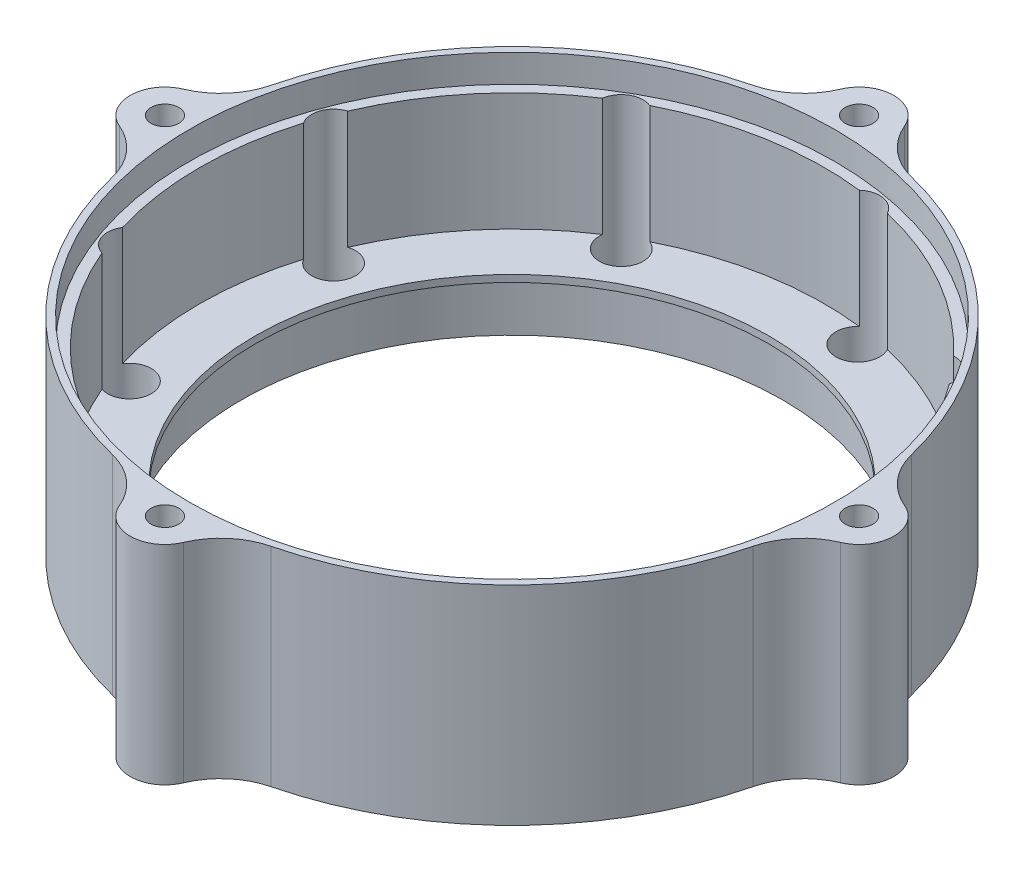
SolidWorks part; units mm, degrees
material "PET"
ref_plane "Front Plane" through (0, 0, 0) normal (0, 0, 1) x (1, 0, 0)
ref_plane "Top Plane" through (0, 0, 0) normal (0, 1, 0) x (1, 0, 0)
ref_plane "Right Plane" through (0, 0, 0) normal (1, 0, 0) x (0, 0, -1)
sketch "Sketch1" plane through (0, 0, 0) normal (0, 1, 0) x (1, 0, 0)
  line L0 (0, 0) -> (50, 0) construction
  circle A0 centre (0, 0) radius 50
  dimension "D1" = 100
extrude "Boss-Extrude1" add sketch "Sketch1" along normal blind 5
sketch "Sketch2" plane through (0, 5, 0) normal (0, 1, 0) x (1, 0, 0)
  line L0 (0, 0) -> (50, 0) construction
  circle A0 centre (0, 0) radius 50 construction
  circle A1 centre (43, 0) radius 3
  circle A2 centre (32.9399, -27.6399) radius 3
  circle A3 centre (7.4669, -42.3467) radius 3
  circle A4 centre (-21.5, -37.2391) radius 3
  circle A5 centre (-40.4068, -14.7069) radius 3
  circle A6 centre (-40.4068, 14.7069) radius 3
  circle A7 centre (-21.5, 37.2391) radius 3
  circle A8 centre (7.4669, 42.3467) radius 3
  circle A9 centre (32.9399, 27.6399) radius 3
  point P30 (0, 0)
  dimension "D1" = 6
  dimension "D2" = 43
  dimension "D3" = 9
extrude "Boss-Extrude2" add sketch "Sketch2" along normal blind 30
sketch "Sketch3" plane through (0, 5, 0) normal (0, 1, 0) x (1, 0, 0)
  circle A45 centre (0, 0) radius 50
  arc A46 (45.9186, 2.7353) -> (36.9339, 27.4206) centre (0, 0) ccw
  arc A50 (45.9186, -2.7353) -> (45.9186, 2.7353) centre (43, 0) ccw
  arc A60 (33.4175, -31.6113) -> (36.9339, -27.4206) centre (32.9399, -27.6399) ccw
  arc A69 (5.28, -45.696) -> (10.6674, -44.746) centre (7.4669, -42.3467) ccw
  arc A70 (-25.3281, -38.399) -> (-20.5905, -41.1343) centre (-21.5, -37.2391) ccw
  arc A71 (-44.0849, -13.1348) -> (-42.2139, -18.2754) centre (-40.4068, -14.7069) ccw
  arc A72 (-42.2139, 18.2754) -> (-44.0849, 13.1348) centre (-40.4068, 14.7069) ccw
  arc A73 (-20.5905, 41.1343) -> (-25.3281, 38.399) centre (-21.5, 37.2391) ccw
  arc A74 (10.6674, 44.746) -> (5.28, 45.696) centre (7.4669, 42.3467) ccw
  arc A75 (36.9339, 27.4206) -> (33.4175, 31.6113) centre (32.9399, 27.6399) ccw
  arc A76 (36.9339, -27.4206) -> (45.9186, -2.7353) centre (0, 0) ccw
  arc A77 (10.6674, -44.746) -> (33.4175, -31.6113) centre (0, 0) ccw
  arc A78 (-20.5905, -41.1343) -> (5.28, -45.696) centre (0, 0) ccw
  arc A79 (-42.2139, -18.2754) -> (-25.3281, -38.399) centre (0, 0) ccw
  arc A80 (-44.0849, 13.1348) -> (-44.0849, -13.1348) centre (0, 0) ccw
  arc A81 (-25.3281, 38.399) -> (-42.2139, 18.2754) centre (0, 0) ccw
  arc A82 (5.28, 45.696) -> (-20.5905, 41.1343) centre (0, 0) ccw
  arc A83 (33.4175, 31.6113) -> (10.6674, 44.746) centre (0, 0) ccw
  point P25 (0, 0)
  dimension "D1" = 100
  dimension "D2" = 4
extrude "Boss-Extrude3" add sketch "Sketch3" along normal blind 28
sketch "Sketch4" plane through (0, 5, 0) normal (0, 1, 0) x (1, 0, 0)
  circle A0 centre (0, 0) radius 39
  dimension "D1" = 78
extrude "Cut-Extrude1" cut sketch "Sketch4" against normal blind 6
sketch "Sketch5" plane through (0, 5, 0) normal (0, 1, 0) x (1, 0, 0)
  circle A0 centre (43, 0) radius 3
  circle A1 centre (32.9399, -27.6399) radius 3
  circle A2 centre (7.4669, -42.3467) radius 3
  circle A3 centre (-21.5, -37.2391) radius 3
  circle A4 centre (-40.4068, -14.7069) radius 3
  circle A5 centre (-40.4068, 14.7069) radius 3
  circle A6 centre (-21.5, 37.2391) radius 3
  circle A7 centre (7.4669, 42.3467) radius 3
  circle A8 centre (32.9399, 27.6399) radius 3
  point P26 (0, 0)
  dimension "D1" = 9
extrude "Cut-Extrude2" cut sketch "Sketch5" along normal mid plane 88
sketch "Sketch6" plane through (0, 0, 0) normal (0, -1, 0) x (1, 0, 0)
  circle A0 centre (0, 0) radius 39
  circle A1 centre (0, 0) radius 50
extrude "Boss-Extrude4" add sketch "Sketch6" against normal blind 3
sketch "Sketch7" plane through (0, 33, 0) normal (0, 1, 0) x (1, 0, 0)
  circle A1 centre (0, 0) radius 47
  circle A2 centre (0, 0) radius 46
  dimension "D1" = 92
  dimension "D2" = 94
extrude "Cut-Extrude3" cut sketch "Sketch7" against normal blind 4
sketch "Sketch8" plane through (0, 0, 0) normal (0, -1, 0) x (1, 0, 0)
  circle A0 centre (0, 0) radius 39
  circle A1 centre (0, 0) radius 37
  dimension "D1" = 2
extrude "Boss-Extrude5" add sketch "Sketch8" against normal blind 1
sketch "Sketch9" plane through (0, 33, 0) normal (0, 1, 0) x (1, 0, 0)
  line L1 (0, 0) -> (0, 52) construction
  line L3 (0, 0) -> (52, 0) construction
  circle A0 centre (52, 0) radius 2
  circle A2 centre (52, 0) radius 5
  circle A3 centre (-52, 0) radius 2
  circle A4 centre (-52, 0) radius 5
  circle A5 centre (0, 52) radius 2
  circle A6 centre (0, 52) radius 5
  circle A7 centre (0, -52) radius 2
  circle A8 centre (0, -52) radius 5
  dimension "D2" = 4
  dimension "D1" = 52
  dimension "D4" = 4
  dimension "D5" = 3
  dimension "D6" = 52
  dimension "D3" = 3
extrude "Boss-Extrude6" add sketch "Sketch9" against normal up to surface (33 mm away) up to face at (0, 0, 50)
fillet "Fillet1" radius 5 8 edges at (4.489, 16.5, -49.7981) (-4.489, 16.5, -49.7981) (49.7981, 16.5, 4.489) (49.7981, 16.5, -4.489) (-4.489, 16.5, 49.7981) (4.489, 16.5, 49.7981) (-49.7981, 16.5, -4.489) (-49.7981, 16.5, 4.489)
sketch "Sketch10" plane through (0, 5, 0) normal (0, 1, 0) x (1, 0, 0)
  circle A1 centre (32.9399, -27.6399) radius 3.15
  circle A2 centre (43, 0) radius 3.15
  circle A3 centre (43, 0) radius 3.15
  circle A4 centre (7.4669, -42.3467) radius 3.15
  circle A5 centre (-21.5, -37.2391) radius 3.15
  circle A6 centre (-40.4068, -14.7069) radius 3.15
  circle A7 centre (-40.4068, 14.7069) radius 3.15
  circle A8 centre (-21.5, 37.2391) radius 3.15
  circle A9 centre (7.4669, 42.3467) radius 3.15
  circle A10 centre (32.9399, 27.6399) radius 3.15
  point P22 (0, 0)
  dimension "D1" = 0.15
  dimension "D2" = 9
extrude "Cut-Extrude6" cut sketch "Sketch10" against normal blind 2.5
sketch "Sketch11" plane through (0, 33, 0) normal (0, 1, 0) x (1, 0, 0)
  circle A2 centre (0, 0) radius 47.15
  circle A3 centre (0, 0) radius 47.15
  dimension "D1" = 0.15
extrude "Cut-Extrude7" cut sketch "Sketch11" against normal blind 4
sketch "Sketch12" plane through (0, 5, 0) normal (0, 1, 0) x (1, 0, 0)
  circle A20 centre (0, 0) radius 39
  circle A21 centre (0, 0) radius 39
  circle A22 centre (32.9399, -27.6399) radius 3.15
  circle A23 centre (43, 0) radius 3.15
  circle A24 centre (43, 0) radius 3.15
  circle A25 centre (7.4669, -42.3467) radius 3.15
  circle A26 centre (-21.5, -37.2391) radius 3.15
  circle A27 centre (-40.4068, -14.7069) radius 3.15
  circle A28 centre (-40.4068, 14.7069) radius 3.15
  circle A29 centre (-21.5, 37.2391) radius 3.15
  circle A30 centre (7.4669, 42.3467) radius 3.15
  circle A31 centre (32.9399, 27.6399) radius 3.15
  arc A36 (36.9339, -27.4206) -> (45.9186, -2.7353) centre (0, 0) ccw
  arc A37 (45.9186, -2.7353) -> (45.9186, 2.7353) centre (43, 0) ccw
  arc A38 (45.9186, 2.7353) -> (36.9339, 27.4206) centre (0, 0) ccw
  arc A39 (36.9339, 27.4206) -> (33.4175, 31.6113) centre (32.9399, 27.6399) ccw
  arc A40 (33.4175, 31.6113) -> (10.6674, 44.746) centre (0, 0) ccw
  arc A41 (10.6674, 44.746) -> (5.28, 45.696) centre (7.4669, 42.3467) ccw
  arc A42 (5.28, 45.696) -> (-20.5905, 41.1343) centre (0, 0) ccw
  arc A43 (-20.5905, 41.1343) -> (-25.3281, 38.399) centre (-21.5, 37.2391) ccw
  arc A44 (-25.3281, 38.399) -> (-42.2139, 18.2754) centre (0, 0) ccw
  arc A45 (-42.2139, 18.2754) -> (-44.0849, 13.1348) centre (-40.4068, 14.7069) ccw
  arc A46 (-44.0849, 13.1348) -> (-44.0849, -13.1348) centre (0, 0) ccw
  arc A47 (-44.0849, -13.1348) -> (-42.2139, -18.2754) centre (-40.4068, -14.7069) ccw
  arc A48 (-42.2139, -18.2754) -> (-25.3281, -38.399) centre (0, 0) ccw
  arc A49 (-25.3281, -38.399) -> (-20.5905, -41.1343) centre (-21.5, -37.2391) ccw
  arc A50 (-20.5905, -41.1343) -> (5.28, -45.696) centre (0, 0) ccw
  arc A51 (5.28, -45.696) -> (10.6674, -44.746) centre (7.4669, -42.3467) ccw
  arc A52 (10.6674, -44.746) -> (33.4175, -31.6113) centre (0, 0) ccw
  arc A53 (33.4175, -31.6113) -> (36.9339, -27.4206) centre (32.9399, -27.6399) ccw
  arc A54 (36.9339, -27.4206) -> (45.9186, -2.7353) centre (0, 0) ccw
  arc A55 (45.9186, -2.7353) -> (45.9186, 2.7353) centre (43, 0) ccw
  arc A56 (45.9186, 2.7353) -> (36.9339, 27.4206) centre (0, 0) ccw
  arc A57 (36.9339, 27.4206) -> (33.4175, 31.6113) centre (32.9399, 27.6399) ccw
  arc A58 (33.4175, 31.6113) -> (10.6674, 44.746) centre (0, 0) ccw
  arc A59 (10.6674, 44.746) -> (5.28, 45.696) centre (7.4669, 42.3467) ccw
  arc A60 (5.28, 45.696) -> (-20.5905, 41.1343) centre (0, 0) ccw
  arc A61 (-20.5905, 41.1343) -> (-25.3281, 38.399) centre (-21.5, 37.2391) ccw
  arc A62 (-25.3281, 38.399) -> (-42.2139, 18.2754) centre (0, 0) ccw
  arc A63 (-42.2139, 18.2754) -> (-44.0849, 13.1348) centre (-40.4068, 14.7069) ccw
  arc A64 (-44.0849, 13.1348) -> (-44.0849, -13.1348) centre (0, 0) ccw
  arc A65 (-44.0849, -13.1348) -> (-42.2139, -18.2754) centre (-40.4068, -14.7069) ccw
  arc A66 (-42.2139, -18.2754) -> (-25.3281, -38.399) centre (0, 0) ccw
  arc A67 (-25.3281, -38.399) -> (-20.5905, -41.1343) centre (-21.5, -37.2391) ccw
  arc A68 (-20.5905, -41.1343) -> (5.28, -45.696) centre (0, 0) ccw
  arc A69 (5.28, -45.696) -> (10.6674, -44.746) centre (7.4669, -42.3467) ccw
  arc A70 (10.6674, -44.746) -> (33.4175, -31.6113) centre (0, 0) ccw
  arc A71 (33.4175, -31.6113) -> (36.9339, -27.4206) centre (32.9399, -27.6399) ccw
  point P45 (0, 0)
  dimension "D1" = 0
  dimension "D2" = 0
  dimension "D3" = 0
  dimension "D4" = 9
extrude "Boss-Extrude7" add sketch "Sketch12" along normal blind 7
sketch "Sketch13" plane through (0, 12, 0) normal (0, 1, 0) x (1, 0, 0)
  circle A0 centre (0, 0) radius 39
  circle A1 centre (0, 0) radius 39
  circle A4 centre (0, 0) radius 37
  circle A5 centre (0, 0) radius 37
  circle M7 centre (0, 0) radius 39
  dimension "D1" = 0
  dimension "D2" = 0
extrude "Boss-Extrude9" add sketch "Sketch13" against normal blind 1 contours A5 M7
sketch "Sketch14" plane through (0, 0, 0) normal (0, -1, 0) x (1, 0, 0)
  circle A0 centre (0, 0) radius 37
  circle A1 centre (0, 0) radius 39
  dimension "D1" = 2
extrude "Cut-Extrude8" cut sketch "Sketch14" against normal blind 1
sketch "Sketch15" plane through (0, 2.5, 0) normal (0, 1, 0) x (1, 0, 0)
  circle A0 centre (43, 0) radius 3.15
  circle A1 centre (32.9399, -27.6399) radius 3.15
  circle A2 centre (7.4669, -42.3467) radius 3.15
  circle A3 centre (-21.5, -37.2391) radius 3.15
  circle A4 centre (-40.4068, -14.7069) radius 3.15
  circle A5 centre (-40.4068, 14.7069) radius 3.15
  circle A6 centre (-21.5, 37.2391) radius 3.15
  circle A7 centre (7.4669, 42.3467) radius 3.15
  circle A8 centre (32.9399, 27.6399) radius 3.15
  point P22 (0, 0)
  dimension "D1" = 9
extrude "Boss-Extrude10" add sketch "Sketch15" along normal blind 2.9
sketch "Sketch16" plane through (0, 0, 0) normal (0, -1, 0) x (-1, 0, 0)
  circle A0 centre (0, 0) radius 57
extrude "Cut-Extrude9" cut sketch "Sketch16" against normal blind 3
sketch "Sketch17" plane through (0, 29, 0) normal (0, 1, 0) x (1, 0, 0)
  circle A1 centre (0, 0) radius 47.15
  arc A2 (44.9311, 2.4886) -> (36.0189, 26.9748) centre (0, 0) ccw
  arc A3 (45.9186, 2.7353) -> (36.9339, 27.4206) centre (0, 0) ccw construction
  circle A4 centre (43, 0) radius 3.15
  circle A5 centre (32.9399, -27.6399) radius 3.15
  circle A6 centre (7.4669, -42.3467) radius 3.15
  circle A7 centre (-21.5, -37.2391) radius 3.15
  circle A8 centre (-40.4068, -14.7069) radius 3.15
  circle A9 centre (-40.4068, 14.7069) radius 3.15
  circle A10 centre (-21.5, 37.2391) radius 3.15
  circle A11 centre (7.4669, 42.3467) radius 3.15
  circle A12 centre (32.9399, 27.6399) radius 3.15
  arc A13 (32.8196, 30.7876) -> (10.253, 43.8164) centre (0, 0) ccw
  arc A14 (5.3514, 44.6807) -> (-20.3104, 40.1558) centre (0, 0) ccw
  arc A15 (-24.6208, 37.6672) -> (-41.3703, 17.7059) centre (0, 0) ccw
  arc A16 (-43.0726, 13.0288) -> (-43.0726, -13.0288) centre (0, 0) ccw
  arc A17 (-41.3703, -17.7059) -> (-24.6208, -37.6672) centre (0, 0) ccw
  arc A18 (-20.3104, -40.1558) -> (5.3514, -44.6807) centre (0, 0) ccw
  arc A19 (10.253, -43.8164) -> (32.8196, -30.7876) centre (0, 0) ccw
  arc A20 (36.0189, -26.9748) -> (44.9311, -2.4886) centre (0, 0) ccw
  point P30 (0, 0)
  arc M3 (45.9186, -2.7353) -> (36.9339, -27.4206) centre (0, 0) cw
  arc M4 (36.9339, -27.4206) -> (33.4175, -31.6113) centre (32.9399, -27.6399) cw
  arc M5 (33.4175, -31.6113) -> (10.6674, -44.746) centre (0, 0) cw
  arc M6 (10.6674, -44.746) -> (5.28, -45.696) centre (7.4669, -42.3467) cw
  arc M7 (5.28, -45.696) -> (-20.5905, -41.1343) centre (0, 0) cw
  arc M8 (-20.5905, -41.1343) -> (-25.3281, -38.399) centre (-21.5, -37.2391) cw
  arc M9 (-25.3281, -38.399) -> (-42.2139, -18.2754) centre (0, 0) cw
  arc M10 (-42.2139, -18.2754) -> (-44.0849, -13.1348) centre (-40.4068, -14.7069) cw
  arc M11 (-44.0849, -13.1348) -> (-44.0849, 13.1348) centre (0, 0) cw
  arc M12 (-44.0849, 13.1348) -> (-42.2139, 18.2754) centre (-40.4068, 14.7069) cw
  arc M13 (-42.2139, 18.2754) -> (-25.3281, 38.399) centre (0, 0) cw
  arc M14 (-25.3281, 38.399) -> (-20.5905, 41.1343) centre (-21.5, 37.2391) cw
  arc M15 (-20.5905, 41.1343) -> (5.28, 45.696) centre (0, 0) cw
  arc M16 (5.28, 45.696) -> (10.6674, 44.746) centre (7.4669, 42.3467) cw
  arc M17 (10.6674, 44.746) -> (33.4175, 31.6113) centre (0, 0) cw
  arc M18 (33.4175, 31.6113) -> (36.9339, 27.4206) centre (32.9399, 27.6399) cw
  arc M19 (36.9339, 27.4206) -> (45.9186, 2.7353) centre (0, 0) cw
  arc M20 (45.9186, 2.7353) -> (45.9186, -2.7353) centre (43, 0) cw
  dimension "D1" = 1
  dimension "D2" = 9
extrude "Boss-Extrude11" add sketch "Sketch17" against normal up to surface (17 mm away) contours A20 A5 A19 A6 A18 A7 A17 A8 A16 A9 A15 A10 A14 A11 A13 A12 A2 A4 M3 M20 M19 M18 M17 M16 M15 M14 M13 M12 M11 M10 M9 M8 M7 M6 M5 M4
sketch "Sketch18" plane through (0, 33, 0) normal (0, 1, 0) x (1, 0, 0)
  circle A0 centre (0, 0) radius 60
  circle A4 centre (0, 0) radius 50
  circle A5 centre (0, 0) radius 47.5
  circle M4 centre (0, -52) radius 2
  arc M5 (-49.2045, -8.8833) -> (-8.8833, -49.2045) centre (0, 0) ccw
  arc M6 (-8.8833, -49.2045) -> (-4.8858, -53.0625) centre (-9.7716, -54.125) cw
  arc M7 (-4.8858, -53.0625) -> (4.8858, -53.0625) centre (0, -52) ccw
  arc M8 (4.8858, -53.0625) -> (8.8833, -49.2045) centre (9.7716, -54.125) cw
  arc M9 (8.8833, -49.2045) -> (49.2045, -8.8833) centre (0, 0) ccw
  arc M10 (49.2045, -8.8833) -> (53.0625, -4.8858) centre (54.125, -9.7716) cw
  arc M11 (53.0625, -4.8858) -> (53.0625, 4.8858) centre (52, 0) ccw
  arc M12 (53.0625, 4.8858) -> (49.2045, 8.8833) centre (54.125, 9.7716) cw
  arc M13 (49.2045, 8.8833) -> (8.8833, 49.2045) centre (0, 0) ccw
  arc M14 (8.8833, 49.2045) -> (4.8858, 53.0625) centre (9.7716, 54.125) cw
  arc M15 (4.8858, 53.0625) -> (-4.8858, 53.0625) centre (0, 52) ccw
  arc M16 (-4.8858, 53.0625) -> (-8.8833, 49.2045) centre (-9.7716, 54.125) cw
  arc M17 (-8.8833, 49.2045) -> (-49.2045, 8.8833) centre (0, 0) ccw
  arc M18 (-49.2045, 8.8833) -> (-53.0625, 4.8858) centre (-54.125, 9.7716) cw
  arc M19 (-53.0625, 4.8858) -> (-53.0625, -4.8858) centre (-52, 0) ccw
  arc M20 (-53.0625, -4.8858) -> (-49.2045, -8.8833) centre (-54.125, -9.7716) cw
  circle M21 centre (52, 0) radius 2
  circle M22 centre (-52, 0) radius 2
  circle M23 centre (0, 52) radius 2
  dimension "D2" = 120
  dimension "D1" = 2.5
extrude "Cut-Extrude13" cut sketch "Sketch18" against normal up to surface (30 mm away) contours A0 M5 M20 M19 M18 M17 M16 M15 M14 M13 M12 M11 M10 M9 M8 M7 M6 | A4 A5 M9 M13 M17 M5 | A4 M4 M6 M7 M8 | A4 M10 M11 M12 M21 | A4 M14 M15 M16 M23 | A4 M18 M19 M20 M22
sketch "Sketch19" plane through (0, 12, 0) normal (0, 1, 0) x (1, 0, 0)
  circle A0 centre (0, 0) radius 47.15
  circle A1 centre (0, 0) radius 46.15
  dimension "D1" = 1
extrude "Boss-Extrude12" add sketch "Sketch19" along normal up to surface (21 mm away) up to face at (0, 33, 47.15)
sketch "Sketch20" plane through (0, 33, 0) normal (0, 1, 0) x (1, 0, 0)
  circle A4 centre (0, 0) radius 47.5
  circle A5 centre (0, 0) radius 46.5
  circle M3 centre (0, 0) radius 46.15
  dimension "D1" = 95
  dimension "D2" = 1
extrude "Cut-Extrude14" cut sketch "Sketch20" against normal up to surface (4 mm away) contours A5 M3 up to face at (-7.7372, 29, 43.8801)
sketch "Sketch21" plane through (0, 33, 0) normal (0, 1, 0) x (1, 0, 0)
  line L0 (0, 0) -> (50, 0) construction
  line L1 (0, 0) -> (51.9264, 0) construction
  circle A0 centre (50, 0) radius 2
  circle A1 centre (0, -50) radius 2
  circle A2 centre (-50, 0) radius 2
  circle A3 centre (0, 50) radius 2
  circle A6 centre (50, 0) radius 5
  circle A7 centre (0, -50) radius 5
  circle A8 centre (-50, 0) radius 5
  circle A9 centre (0, 50) radius 5
  point P14 (0, 0)
  point P22 (0, 0)
  circle M9 centre (0, 0) radius 47.5
  dimension "D1" = 4
  dimension "D4" = 10
  dimension "D6" = 4
  dimension "D2" = 0
  dimension "D5" = 50
  dimension "D3" = 4
extrude "Boss-Extrude14" add sketch "Sketch21" against normal up to surface (30 mm away) contours A8 A2 M9 | A7 A1 M9 | A6 A0 M9 | A9 A3 M9
fillet "Fillet2" radius 10 8 edges at (-47.3125, 18, -4.2163) (-47.3125, 18, 4.2163) (4.2163, 18, -47.3125) (-4.2163, 18, -47.3125) (47.3125, 18, 4.2163) (47.3125, 18, -4.2163) (-4.2163, 18, 47.3125) (4.2163, 18, 47.3125)
